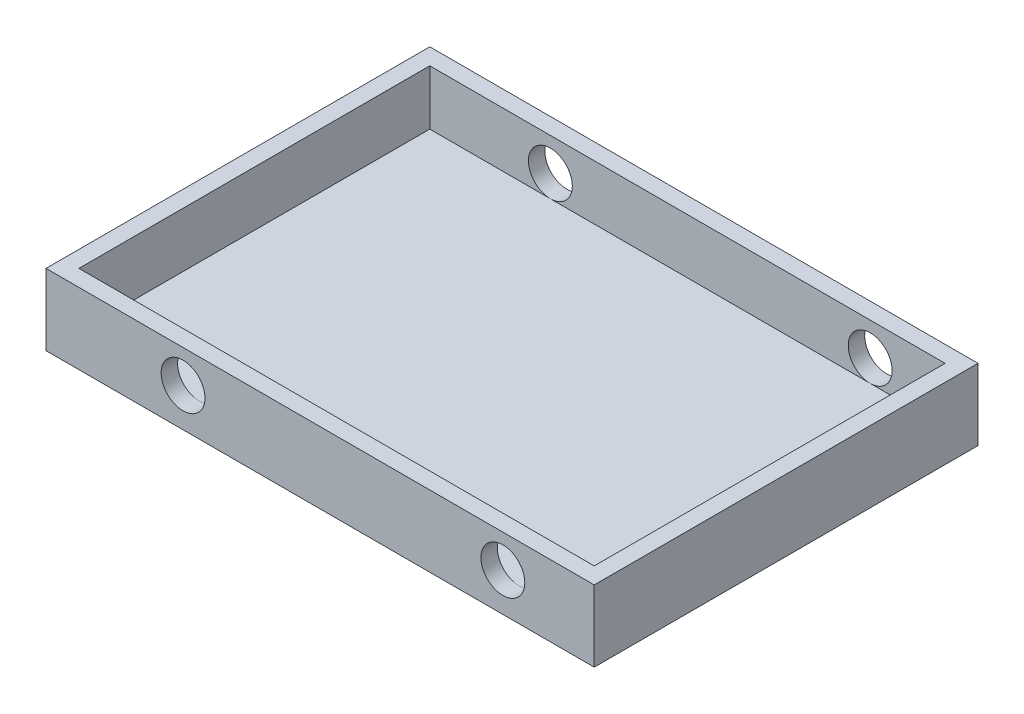
SolidWorks part; units mm, degrees
ref_plane "Alzado" through (0, 0, 0) normal (0, 0, 1) x (1, 0, 0)
ref_plane "Planta" through (0, 0, 0) normal (0, 1, 0) x (1, 0, 0)
ref_plane "Vista lateral" through (0, 0, 0) normal (1, 0, 0) x (0, 0, -1)
sketch "Croquis1" plane through (0, 0, 0) normal (0, 1, 0) x (1, 0, 0)
  line L1 (-250, 175) -> (250, 175)
  line L2 (-250, 175) -> (-250, -175)
  line L3 (-250, -175) -> (250, -175)
  line L4 (250, 175) -> (250, -175)
  line L5 (-250, 175) -> (250, -175) construction
  line L6 (-250, -175) -> (250, 175) construction
  point P0 (0, 0)
  dimension "D1" = 350
  dimension "D2" = 500
extrude "Saliente-Extruir1" add sketch "Croquis1" along normal blind 15
sketch "Croquis2" plane through (0, 15, 0) normal (0, 1, 0) x (1, 0, 0)
  line L0 (-235, 160) -> (235, 160)
  line L1 (-250, 175) -> (250, 175)
  line L2 (-250, 175) -> (-250, -175)
  line L3 (-250, -175) -> (250, -175)
  line L4 (250, 175) -> (250, -175)
  line L5 (-250, 175) -> (250, -175) construction
  line L6 (-250, -175) -> (250, 175) construction
  line L7 (235, 160) -> (235, -160)
  line L8 (235, -160) -> (-235, -160)
  line L9 (-235, -160) -> (-235, 160)
  point P0 (0, 0)
  dimension "D1" = 15
  dimension "D2" = 15
  dimension "D3" = 15
  dimension "D4" = 15
extrude "Saliente-Extruir2" add sketch "Croquis2" along normal blind 50
sketch "Croquis3" plane through (0, 0, 175) normal (0, 0, 1) x (1, 0, 0)
  line L0 (0, 0) -> (0, 35) construction
  line L1 (0, 35) -> (-125, 35) construction
  line L2 (-125, 35) -> (-250, 35) construction
  line L4 (0, 35) -> (83.3333, 35) construction
  line L5 (83.3333, 35) -> (166.6667, 35) construction
  line L6 (166.6667, 35) -> (250, 35) construction
  line L8 (250, 65) -> (250, 0) construction
  circle A0 centre (-125, 35) radius 20
  circle A1 centre (166.6667, 35) radius 20
  point P6 (0, 0)
  point P7 (0, 0)
  point P11 (250, 40)
  point P14 (0, 0)
  dimension "D1" = 40
  dimension "D2" = 35
extrude "Cortar-Extruir1" cut sketch "Croquis3" against normal through all
